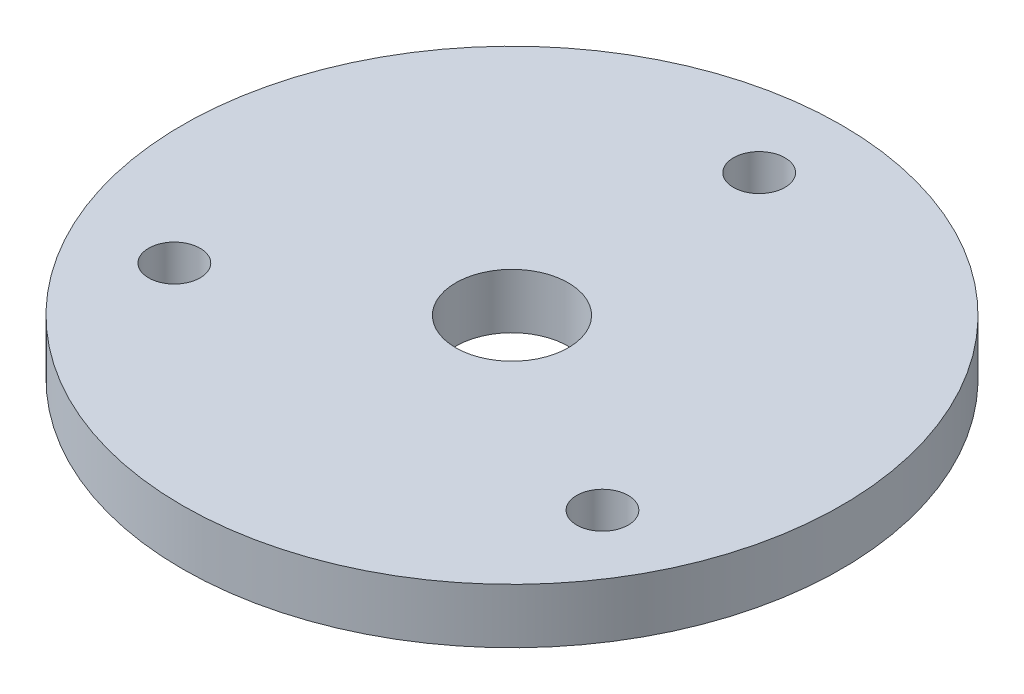
SolidWorks part; units mm, degrees
material "6061 Alloy"
ref_plane "Front Plane" through (0, 0, 0) normal (0, 0, 1) x (1, 0, 0)
ref_plane "Top Plane" through (0, 0, 0) normal (0, 1, 0) x (1, 0, 0)
ref_plane "Right Plane" through (0, 0, 0) normal (1, 0, 0) x (0, 0, -1)
sketch "Sketch1" plane through (0, 0, 0) normal (0, 0, 1) x (1, 0, 0)
  line L1 (-76.2, 0) -> (76.2, 0) construction
  dimension "OD" = 152.4
sketch "Sketch2" plane through (0, 0, 0) normal (0, 0, 1) x (1, 0, 0)
  line L0 (0, -6.35) -> (0, 6.35)
  point P4 (0, 0)
  dimension "Thickness" = 12.7
sketch "Sketch3" plane through (0, 0, 0) normal (0, 1, 0) x (1, 0, 0)
  circle A0 centre (0, 0) radius 76.2
extrude "Boss-Extrude1" add sketch "Sketch3" along normal up to vertex (6.35 mm away) and the other way up to vertex (6.35 mm away) up to point (0, 6.35, 0) other way up to point (0, -6.35, 0)
sketch "Sketch4" plane through (0, 6.35, 0) normal (0, 1, 0) x (1, 0, 0)
  circle A0 centre (0, 0) radius 13.0175
  circle A1 centre (0, 0) radius 57.15 construction
  circle A2 centre (0, 57.15) radius 5.9531
  circle A3 centre (49.4934, -28.575) radius 5.9531
  circle A4 centre (-49.4934, -28.575) radius 5.9531
  point P13 (0, 0)
  dimension "D1" = 26.035
  dimension "D2" = 114.3
  dimension "D3" = 11.9062
  dimension "D4" = 3
extrude "Cut-Extrude1" cut sketch "Sketch4" against normal through all
